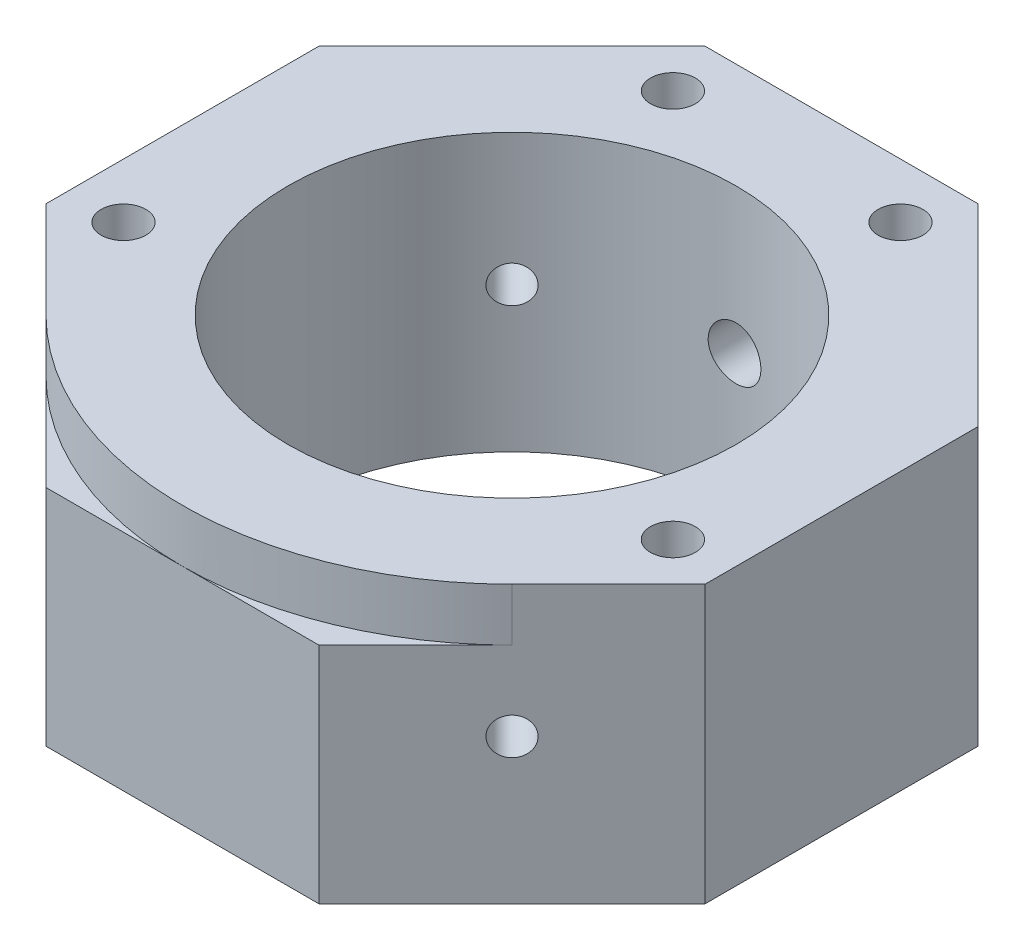
SolidWorks part; units mm, degrees
ref_plane "Front Plane" through (0, 0, 0) normal (0, 0, 1) x (1, 0, 0)
ref_plane "Top Plane" through (0, 0, 0) normal (0, 1, 0) x (1, 0, 0)
ref_plane "Right Plane" through (0, 0, 0) normal (1, 0, 0) x (0, 0, -1)
sketch "Sketch1" plane through (0, 0, 0) normal (0, 1, 0) x (1, 0, 0)
  line L0 (25, -10.3553) -> (25, 10.3553)
  line L1 (10.3553, 25) -> (-10.3553, 25)
  line L2 (-10.3553, 25) -> (-25, 10.3553)
  line L3 (-25, 10.3553) -> (-25, -10.3553)
  line L4 (-25, -10.3553) -> (-10.3553, -25)
  line L5 (-10.3553, -25) -> (10.3553, -25)
  line L6 (10.3553, -25) -> (25, -10.3553)
  line L7 (25, 10.3553) -> (10.3553, 25)
  circle A0 centre (0, 0) radius 25 construction
  circle A1 centre (0, 0) radius 17
  dimension "D2" = 34
  dimension "D1" = 50
extrude "Boss-Extrude1" add sketch "Sketch1" along normal blind 21
sketch "Sketch2" plane through (0, 21, 0) normal (0, 1, 0) x (1, 0, 0)
  line L4 (22, 9.1127) -> (9.1127, 22)
  line L5 (9.1127, 22) -> (-9.1127, 22)
  line L6 (-9.1127, 22) -> (-22, 9.1127)
  line L7 (-22, 9.1127) -> (-22, -9.1127)
  line L8 (-22, -9.1127) -> (-9.1127, -22)
  line L9 (-9.1127, -22) -> (9.1127, -22)
  line L10 (9.1127, -22) -> (22, -9.1127)
  line L11 (22, -9.1127) -> (22, 9.1127)
  line L12 (25, 10.3553) -> (10.3553, 25)
  line L13 (10.3553, 25) -> (-10.3553, 25)
  line L14 (-10.3553, 25) -> (-25, 10.3553)
  line L15 (-25, 10.3553) -> (-25, -10.3553)
  line L16 (-25, -10.3553) -> (-10.3553, -25)
  line L17 (-10.3553, -25) -> (10.3553, -25)
  line L18 (10.3553, -25) -> (25, -10.3553)
  line L19 (25, -10.3553) -> (25, 10.3553)
  line L20 (25, 10.3553) -> (10.3553, 25) construction
  line L21 (10.3553, 25) -> (-10.3553, 25) construction
  line L22 (-10.3553, 25) -> (-25, 10.3553) construction
  line L23 (-25, 10.3553) -> (-25, -10.3553) construction
  line L24 (-25, -10.3553) -> (-10.3553, -25) construction
  line L25 (-10.3553, -25) -> (10.3553, -25) construction
  line L26 (10.3553, -25) -> (25, -10.3553) construction
  line L27 (25, -10.3553) -> (25, 10.3553) construction
  circle A2 centre (0, 0) radius 17 construction
  circle A3 centre (0, 0) radius 17
  dimension "D1" = 0
  dimension "D2" = 3
extrude "Boss-Extrude2" [suppressed] add sketch "Sketch2" along normal blind 8
sketch "Sketch4" [suppressed] plane through (0, 29, 0) normal (0, 1, 0) x (1, 0, 0)
  line L0 (-16.0513, 11.5258) -> (-12.6252, 8.0997)
  line L1 (-8.0772, 19.5) -> (-19.5, 8.0772) construction
  line L2 (-12.6252, 8.0997) -> (12.6252, 8.0997)
  line L3 (12.6252, 8.0997) -> (16.0513, 11.5258)
  line L4 (19.5, 8.0772) -> (8.0772, 19.5) construction
  line L5 (16.0513, 11.5258) -> (8.0772, 19.5)
  line L6 (8.0772, 19.5) -> (-8.0772, 19.5)
  line L7 (-8.0772, 19.5) -> (-16.0513, 11.5258)
  line L8 (0, 0) -> (-13.7886, 13.7886) construction
  circle A0 centre (0, 0) radius 15 construction
  dimension "D1" = 3.2
extrude "Cut-Extrude1" [suppressed] cut sketch "Sketch4" against normal up to surface (8 mm away)
sketch "Sketch5" [suppressed] plane through (0, 29, 0) normal (0, 1, 0) x (1, 0, 0)
  circle A0 centre (0, 0) radius 17
  arc A1 (-12.6252, 8.0997) -> (12.6252, 8.0997) centre (0, 0) ccw construction
  dimension "D1" = 2
extrude "Cut-Extrude2" [suppressed] cut sketch "Sketch5" against normal up to surface (8 mm away)
hole_wizard "CBORE for M3 Hex Socket Head Cap Screw1" positions "Sketch6" profile "Sketch7" counterbore size "M3" standard "DIN" end condition up to next
sketch "Sketch6" plane through (0, 0, 0) normal (0, -1, 0) x (-1, 0, 0)
  line L0 (-10.3553, 25) -> (-8.6333, 20.8425) construction
  line L1 (-8.6333, 20.8425) -> (0, 0) construction
  line L2 (0, 0) -> (-20.8425, -8.6333) construction
  line L3 (-20.8425, -8.6333) -> (-25, -10.3553) construction
  line L6 (25, -10.3553) -> (20.8425, -8.6333) construction
  line L7 (20.8425, -8.6333) -> (0, 0) construction
  line L9 (8.6333, 20.8425) -> (0, 0) construction
  line L11 (8.6333, 20.8425) -> (10.3553, 25) construction
  point P0 (20.8425, -8.6333)
  point P2 (-20.8425, -8.6333)
  point P4 (8.6333, 20.8425)
  point P6 (-8.6333, 20.8425)
  dimension "D1" = 4.5
sketch "Sketch7" plane through (-20.8425, 0, 8.6333) normal (1, 0, 0) x (0, 0, -1)
  line L0 (0, 0) -> (0, 21)
  line L1 (0, 21) -> (1.7, 21)
  line L3 (1.7, 21) -> (1.7, 3.4)
  line L4 (1.7, 3.4) -> (3.25, 3.4)
  line L5 (3.25, 3.4) -> (3.25, 0)
  line L7 (3.25, 0) -> (0, 0)
  line L11 (0, -6.35) -> (0, 107.95) construction
  dimension "Thru Hole Dia." = 3.4
  dimension "Thru Hole Depth" = 21
  dimension "C'Bore Dia." = 6.5
  dimension "C'Bore Depth" = 3.4
hole_wizard "M3x0.2 Tapped Hole1" positions "Sketch8" profile "Sketch9" tap size "M3x0.2" standard "DIN" end condition through all
sketch "Sketch8" plane through (17.6777, 0, 17.6777) normal (0.7071, 0, 0.7071) x (0.7071, 0, -0.7071)
  line L0 (-10.3553, 0) -> (10.3553, 0) construction
  point P0 (0, 11)
  dimension "D1" = 11
sketch "Sketch9" plane through (17.6777, 11, 17.6777) normal (0, 1, 0) x (0.7071, 0, -0.7071)
  line L0 (0, 0) -> (0, 60.3553)
  line L1 (0, 60.3553) -> (1.4, 60.3553)
  line L2 (1.4, 60.3553) -> (1.4, 0)
  line L5 (1.4, 0) -> (0, 0)
  line L11 (0, -6.35) -> (0, 107.95) construction
  dimension "Thru Tap Drill Dia." = 2.8
  dimension "Thru Tap Drill Depth" = 60.3553
cosmetic thread "Hole Thread1" parameters "D2"=3
hole_wizard "M3x0.2 Tapped Hole2" positions "Sketch10" profile "Sketch11" tap size "M3x0.2" standard "DIN" end condition through all
sketch "Sketch10" plane through (-17.6777, 0, 17.6777) normal (-0.7071, 0, 0.7071) x (0.7071, 0, 0.7071)
  line L0 (-10.3553, 0) -> (10.3553, 0) construction
  point P0 (0, 13.5)
  dimension "D1" = 13.5
sketch "Sketch11" plane through (-17.6777, 13.5, 17.6777) normal (0, 1, 0) x (0.7071, 0, 0.7071)
  line L0 (0, 0) -> (0, 60.3553)
  line L1 (0, 60.3553) -> (1.4, 60.3553)
  line L2 (1.4, 60.3553) -> (1.4, 0)
  line L5 (1.4, 0) -> (0, 0)
  line L11 (0, -6.35) -> (0, 107.95) construction
  dimension "Thru Tap Drill Dia." = 2.8
  dimension "Thru Tap Drill Depth" = 60.3553
cosmetic thread "Hole Thread2" parameters "D2"=3
sketch "Sketch12" plane through (0, 0, -25) normal (0, 0, -1) x (-1, 0, 0)
  circle A0 centre (0, 10) radius 2
  dimension "D1" = 4
  dimension "D2" = 10
extrude "Cut-Extrude3" cut sketch "Sketch12" against normal up to next
sketch "Sketch13" plane through (0, 21, 0) normal (0, 1, 0) x (1, 0, 0)
  line L0 (-25, -10.3553) -> (-10.3553, -25) construction
  line L1 (10.3553, -25) -> (25, -10.3553) construction
  line L2 (17.6777, -17.6777) -> (17.6777, -26.6596)
  line L3 (17.6777, -26.6596) -> (-17.6777, -26.6596)
  line L4 (-17.6777, -26.6596) -> (-17.6777, -17.6777)
  arc A0 (-17.6777, -17.6777) -> (17.6777, -17.6777) centre (0, 0) ccw
extrude "Cut-Extrude4" cut sketch "Sketch13" against normal blind 4
